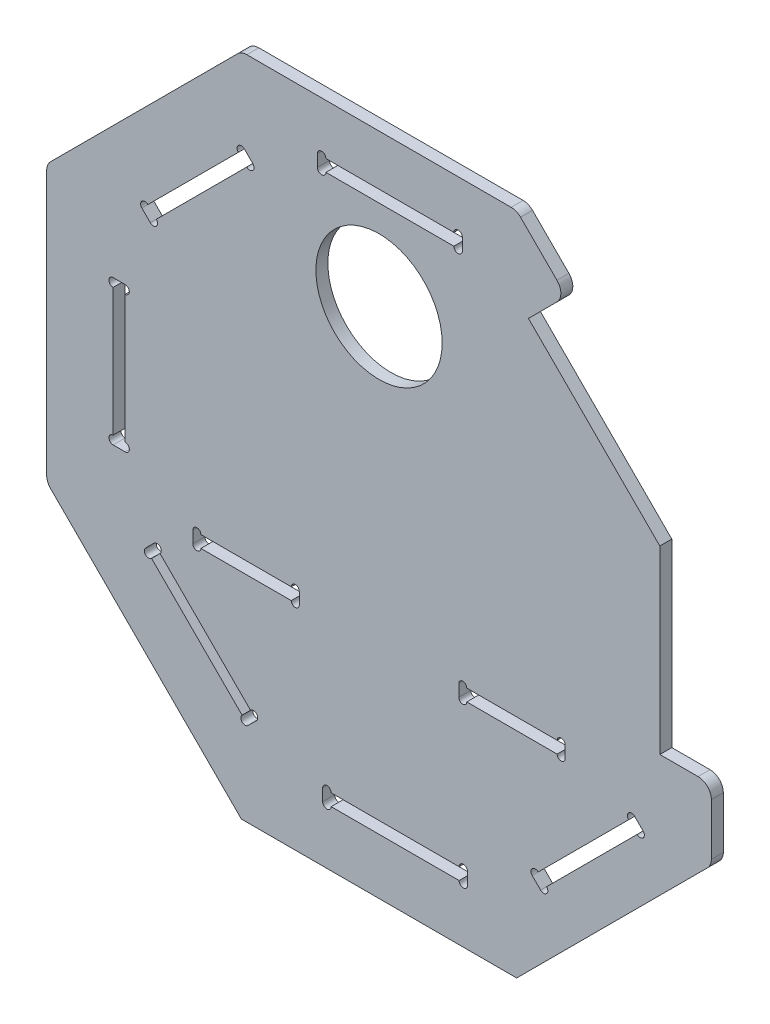
SolidWorks part; units mm, degrees
material "Teak"
ref_plane "Front Plane" through (0, 0, 0) normal (0, 0, 1) x (1, 0, 0)
ref_plane "Top Plane" through (0, 0, 0) normal (0, 1, 0) x (1, 0, 0)
ref_plane "Right Plane" through (0, 0, 0) normal (1, 0, 0) x (0, 0, -1)
sketch "Sketch1" plane through (0, 0, 0) normal (0, 0, 1) x (1, 0, 0)
  line L0 (-191, 0) -> (-200, 0) construction
  line L1 (250, -99.4113) -> (250, -60.5503)
  line L2 (133.8479, 219.7055) -> (106.4823, 247.0711)
  line L3 (99.4113, 250) -> (-99.4113, 250)
  line L4 (-106.4823, 247.0711) -> (-247.0711, 106.4823)
  line L5 (-250, 99.4113) -> (-250, -99.4113)
  line L6 (-247.0711, -106.4823) -> (-103.5534, -250)
  line L7 (-103.5534, -250) -> (103.5534, -250)
  line L8 (103.5534, -250) -> (247.0711, -106.4823)
  line L9 (-200, 54.5) -> (-191, 54.5)
  line L10 (-200, 48.14) -> (-200, -48.14)
  line L11 (-200, -54.5) -> (-191, -54.5)
  line L12 (-191, 48.14) -> (-191, -48.14)
  line L13 (-195.5, 54.5) -> (-195.5, -54.5) construction
  line L14 (-105.8116, 183.2008) -> (-173.8918, 115.1205)
  line L15 (-178.389, 110.6233) -> (-172.025, 104.2594)
  line L16 (-99.4476, 176.8368) -> (-167.5278, 108.7566)
  line L17 (-101.3144, 187.698) -> (-94.9504, 181.334)
  line L18 (56.2921, 212.1019) -> (-39.9879, 212.1019)
  line L19 (-46.3479, 212.1019) -> (-46.3479, 203.1019)
  line L20 (56.2921, 203.1019) -> (-39.9879, 203.1019)
  line L21 (62.6521, 212.1019) -> (62.6521, 203.1019)
  line L23 (133.8479, 205.5633) -> (112.4115, 184.1269)
  line L24 (211.254, 85.2844) -> (112.4115, 184.1269)
  line L28 (211.254, -50.5503) -> (211.254, 85.2844)
  line L29 (240, -50.5503) -> (211.254, -50.5503)
  line L30 (126.0655, -179.251) -> (194.1458, -111.1708)
  line L31 (198.643, -106.6736) -> (192.279, -100.3096)
  line L32 (119.7016, -172.8871) -> (187.7818, -104.8068)
  line L33 (121.5683, -183.7482) -> (115.2044, -177.3843)
  line L34 (-36.0381, -208.1521) -> (60.2419, -208.1521)
  line L35 (66.6019, -208.1521) -> (66.6019, -199.1521)
  line L36 (-36.0381, -199.1521) -> (60.2419, -199.1521)
  line L37 (-42.3981, -208.1521) -> (-42.3981, -199.1521)
  line L38 (-171.0989, -113.9637) -> (-103.0187, -182.0439)
  line L39 (-98.5215, -186.5411) -> (-92.1575, -180.1771)
  line L40 (-164.7349, -107.5997) -> (-96.6547, -175.6799)
  line L41 (-175.5961, -109.4665) -> (-169.2321, -103.1025)
  line L43 (220.254, -44.1903) -> (220.254, 52.0897) [skipped]
  line L44 (220.254, 58.4497) -> (211.254, 58.4497) [skipped]
  line L45 (195.8501, 113.4162) -> (189.4861, 107.0522) [skipped]
  line L46 (191.3529, 117.9134) -> (123.2726, 185.9936) [skipped]
  line L48 (-134, -88.9113) -> (-66, -88.9113)
  line L49 (-140, -88.9113) -> (-140, -79.9113)
  line L50 (-134, -79.9113) -> (-66, -79.9113)
  line L51 (-60, -88.9113) -> (-60, -79.9113)
  line L52 (140, -88.9113) -> (140, -79.9113)
  line L53 (134, -79.9113) -> (66, -79.9113)
  line L54 (-100, -88.9113) -> (-100, -81.365) construction
  line L55 (60, -88.9113) -> (60, -79.9113)
  line L56 (134, -88.9113) -> (66, -88.9113)
  arc A0 (137.2441, 208.9595) -> (244.836, -50.5503) centre (0, 0) ccw construction
  arc A1 (-200, 54.5) -> (-200, 48.14) centre (-200, 51.32) ccw
  arc A2 (-191, 54.5) -> (-191, 48.14) centre (-191, 51.32) cw
  arc A3 (-200, -54.5) -> (-200, -48.14) centre (-200, -51.32) cw
  arc A4 (-191, -54.5) -> (-191, -48.14) centre (-191, -51.32) ccw
  arc A5 (-178.389, 110.6233) -> (-173.8918, 115.1205) centre (-176.1404, 112.8719) cw
  arc A6 (-172.025, 104.2594) -> (-167.5278, 108.7566) centre (-169.7764, 106.508) ccw
  arc A7 (-94.9504, 181.334) -> (-99.4476, 176.8368) centre (-97.199, 179.0854) cw
  arc A8 (-101.3144, 187.698) -> (-105.8116, 183.2008) centre (-103.563, 185.4494) ccw
  arc A9 (-46.3479, 212.1019) -> (-39.9879, 212.1019) centre (-43.1679, 212.1019) cw
  arc A10 (-46.3479, 203.1019) -> (-39.9879, 203.1019) centre (-43.1679, 203.1019) ccw
  arc A11 (62.6521, 203.1019) -> (56.2921, 203.1019) centre (59.4721, 203.1019) cw
  arc A12 (62.6521, 212.1019) -> (56.2921, 212.1019) centre (59.4721, 212.1019) ccw
  arc A21 (198.643, -106.6736) -> (194.1458, -111.1708) centre (196.3944, -108.9222) cw
  arc A22 (192.279, -100.3096) -> (187.7818, -104.8068) centre (190.0304, -102.5582) ccw
  arc A23 (115.2044, -177.3843) -> (119.7016, -172.8871) centre (117.453, -175.1357) cw
  arc A24 (121.5683, -183.7482) -> (126.0655, -179.251) centre (123.8169, -181.4996) ccw
  arc A25 (66.6019, -208.1521) -> (60.2419, -208.1521) centre (63.4219, -208.1521) cw
  arc A26 (66.6019, -199.1521) -> (60.2419, -199.1521) centre (63.4219, -199.1521) ccw
  arc A27 (-42.3981, -199.1521) -> (-36.0381, -199.1521) centre (-39.2181, -199.1521) cw
  arc A28 (-42.3981, -208.1521) -> (-36.0381, -208.1521) centre (-39.2181, -208.1521) ccw
  arc A29 (-98.5215, -186.5411) -> (-103.0187, -182.0439) centre (-100.7701, -184.2925) cw
  arc A30 (-92.1575, -180.1771) -> (-96.6547, -175.6799) centre (-94.4061, -177.9285) ccw
  arc A31 (-169.2321, -103.1025) -> (-164.7349, -107.5997) centre (-166.9835, -105.3511) cw
  arc A32 (-175.5961, -109.4665) -> (-171.0989, -113.9637) centre (-173.3475, -111.7151) ccw
  arc A33 (220.254, -50.5503) -> (220.254, -44.1903) centre (220.254, -47.3703) ccw [skipped]
  arc A34 (220.254, 58.4497) -> (220.254, 52.0897) centre (220.254, 55.2697) cw [skipped]
  arc A35 (211.254, 58.4497) -> (211.254, 52.0897) centre (211.254, 55.2697) ccw [skipped]
  arc A36 (211.254, -50.5503) -> (211.254, -44.1903) centre (211.254, -47.3703) cw [skipped]
  arc A37 (195.8501, 113.4162) -> (191.3529, 117.9134) centre (193.6015, 115.6648) ccw [skipped]
  arc A38 (189.4861, 107.0522) -> (184.9889, 111.5494) centre (187.2375, 109.3008) cw [skipped]
  arc A39 (118.7754, 190.4908) -> (123.2726, 185.9936) centre (121.024, 188.2422) cw [skipped]
  arc A40 (112.4115, 184.1269) -> (116.9087, 179.6297) centre (114.6601, 181.8783) ccw [skipped]
  arc A41 (240, -50.5503) -> (250, -60.5503) centre (240, -60.5503) cw
  arc A42 (133.8479, 205.5633) -> (133.8479, 219.7055) centre (126.7769, 212.6344) ccw
  arc A43 (106.4823, 247.0711) -> (99.4113, 250) centre (99.4113, 240) ccw
  arc A44 (-247.0711, 106.4823) -> (-250, 99.4113) centre (-240, 99.4113) ccw
  arc A45 (-99.4113, 250) -> (-106.4823, 247.0711) centre (-99.4113, 240) ccw
  arc A46 (-250, -99.4113) -> (-247.0711, -106.4823) centre (-240, -99.4113) ccw
  arc A47 (250, -99.4113) -> (247.0711, -106.4823) centre (240, -99.4113) cw
  arc A48 (-140, -88.9113) -> (-134, -88.9113) centre (-137, -88.9113) ccw
  arc A49 (-60, -88.9113) -> (-66, -88.9113) centre (-63, -88.9113) cw
  arc A50 (-140, -79.9113) -> (-134, -79.9113) centre (-137, -79.9113) cw
  arc A51 (-60, -79.9113) -> (-66, -79.9113) centre (-63, -79.9113) ccw
  arc A52 (140, -88.9113) -> (134, -88.9113) centre (137, -88.9113) cw
  arc A53 (140, -79.9113) -> (134, -79.9113) centre (137, -79.9113) ccw
  arc A54 (60, -79.9113) -> (66, -79.9113) centre (63, -79.9113) cw
  arc A55 (60, -88.9113) -> (66, -88.9113) centre (63, -88.9113) ccw
  circle A56 centre (0, 135.632) radius 47.5
  point P69 (-100, -99.4113)
  point P113 (10.127, 1.9749)
  dimension "D1" = 500
  dimension "D5" = 3.18
  dimension "D7" = 10
  dimension "D8" = 10
  dimension "D11" = 3
  dimension "D13" = 95
  dimension "D2" = 9
  dimension "D3" = 50
  dimension "D4" = 109
  dimension "D9" = 9
  dimension "D10" = 150
  dimension "D12" = 80
  dimension "D6" = 8
extrude "Boss-Extrude1" add sketch "Sketch1" along normal mid plane 9
sketch3d "Sketch_MAC1-1_HUGE_MILLING" [suppressed]
  line L0 (-250, -250, 4.5) -> (-240, -250, 4.5)
  line L1 (-250, -250, 4.5) -> (-250, -240, 4.5)
  point P0 (-250, -250, 4.5)
  point P1 (-240, -250, 4.5)
  point P2 (-250, -240, 4.5)
